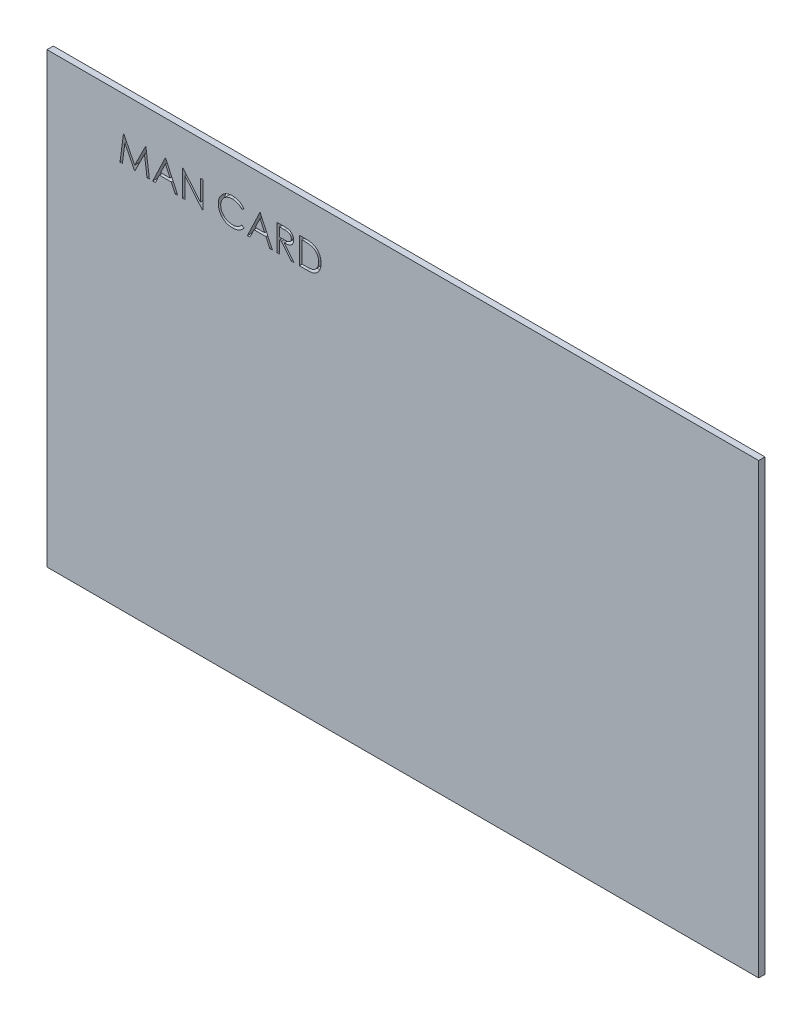
SolidWorks part; units mm, degrees
ref_plane "Front Plane" through (0, 0, 0) normal (0, 0, 1) x (1, 0, 0)
ref_plane "Top Plane" through (0, 0, 0) normal (0, 1, 0) x (1, 0, 0)
ref_plane "Right Plane" through (0, 0, 0) normal (1, 0, 0) x (0, 0, -1)
sketch "Sketch1" plane through (0, 0, 0) normal (0, 0, 1) x (1, 0, 0)
  line L1 (-98.5532, 40.7245) -> (-12.8282, 40.7245)
  line L2 (-98.5532, 40.7245) -> (-98.5532, -13.2505)
  line L3 (-98.5532, -13.2505) -> (-12.8282, -13.2505)
  line L4 (-12.8282, 40.7245) -> (-12.8282, -13.2505)
  dimension "D1" = 53.975
  dimension "D2" = 85.725
extrude "Boss-Extrude1" add sketch "Sketch1" along normal blind 0.7595
sketch "Sketch2" plane through (0, 0, 0.7595) normal (0, 0, 1) x (1, 0, 0)
  text T0 "       MAN CARD" font "Century Gothic" height 3.175
extrude "Cut-Extrude1" cut sketch "Sketch2" against normal blind 0.7595
